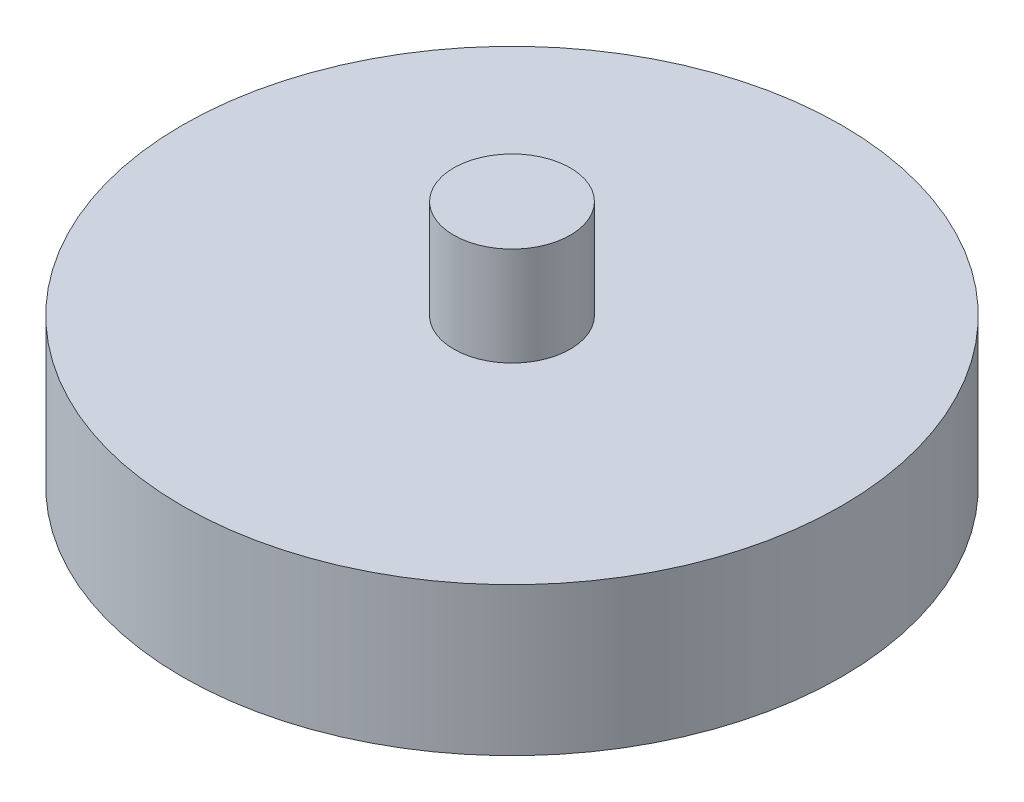
SolidWorks part; units mm, degrees
ref_plane "Front Plane" through (0, 0, 0) normal (0, 0, 1) x (1, 0, 0)
ref_plane "Top Plane" through (0, 0, 0) normal (0, 1, 0) x (1, 0, 0)
ref_plane "Right Plane" through (0, 0, 0) normal (1, 0, 0) x (0, 0, -1)
sketch "Sketch2" plane through (0, 0, 0) normal (0, 1, 0) x (1, 0, 0)
  circle A0 centre (0, 0) radius 33.9325
  point P3 (0, 0)
extrude "Boss-Extrude1" add sketch "Sketch2" along normal blind 15.24
sketch "Sketch3" plane through (0, 0, 0) normal (0, 1, 0) x (1, 0, 0)
  circle A0 centre (0, 0) radius 8.5589
  circle A1 centre (0, 0) radius 6
  circle A2 centre (0, 0) radius 6
extrude "Boss-Extrude2" add sketch "Sketch3" along normal blind 25.4 contours A1
sketch "Sketch4" plane through (0, 0, 0) normal (0, -1, 0) x (1, 0, 0)
  circle A0 centre (0, 0) radius 25.4
extrude "Cut-Extrude1" cut sketch "Sketch4" against normal blind 2.54
